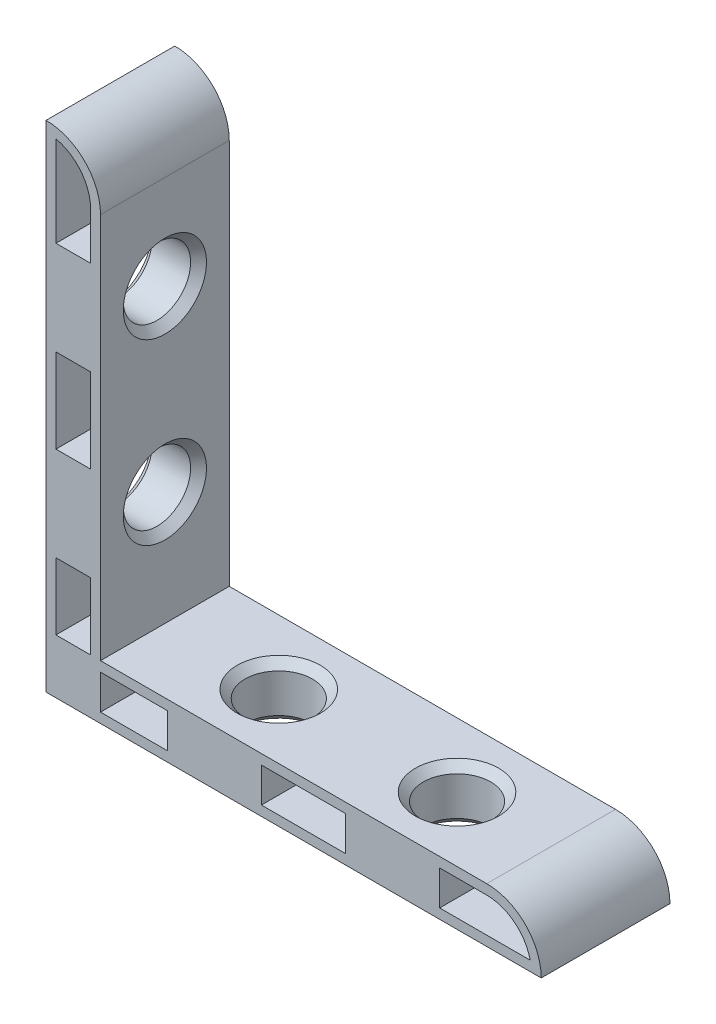
SolidWorks part; units mm, degrees
material "ЦА4М3 ГОСТ 25140-93"
ref_plane "Спереди" through (0, 0, 0) normal (0, 0, 1) x (1, 0, 0)
ref_plane "Сверху" through (0, 0, 0) normal (0, 1, 0) x (1, 0, 0)
ref_plane "Справа" through (0, 0, 0) normal (1, 0, 0) x (0, 0, -1)
sketch "Эскиз1" plane through (0, 0, 0) normal (0, 0, 1) x (1, 0, 0)
  line L0 (0, 50) -> (0, 0)
  line L1 (0, 0) -> (50, 0)
  line L2 (44.5, 5.5) -> (5.5, 5.5)
  line L3 (5.5, 5.5) -> (5.5, 44.5)
  line L4 (1, 48.8875) -> (1, 1)
  line L5 (1, 1) -> (48.8875, 1)
  line L6 (44.5, 4.5) -> (4.5, 4.5)
  line L7 (4.5, 4.5) -> (4.5, 44.5)
  arc A0 (50, 0) -> (44.5, 5.5) centre (44.5, 0) ccw
  arc A1 (5.5, 44.5) -> (0, 50) centre (0, 44.5) ccw
  arc A2 (48.8875, 1) -> (44.5, 4.5) centre (44.5, 0) ccw
  arc A3 (4.5, 44.5) -> (1, 48.8875) centre (0, 44.5) ccw
  point P9 (0, 0)
  dimension "D1" = 50
  dimension "D2" = 5.5
  dimension "D3" = 1
extrude "Бобышка-Вытянуть1" add sketch "Эскиз1" along normal mid plane 13
sketch "Эскиз2" plane through (0, 0, 0) normal (0, 0, 1) x (1, 0, 0)
  line L0 (0, 50) -> (0, 0) construction
  line L1 (5.5, 5.5) -> (0, 5.5)
  line L2 (5.5, 5.5) -> (5.5, 0)
  line L3 (5.5, 0) -> (0, 0)
  line L4 (0, 5.5) -> (0, 0)
  line L5 (0, 39.75) -> (5.5, 39.75)
  line L6 (0, 39.75) -> (0, 30.25)
  line L7 (0, 30.25) -> (5.5, 30.25)
  line L8 (5.5, 39.75) -> (5.5, 30.25)
  line L9 (5.5, 5.5) -> (5.5, 44.5) construction
  line L10 (0, 0) -> (24.8323, 24.8323) construction
  line L11 (0, 21.75) -> (5.5, 21.75)
  line L12 (0, 21.75) -> (0, 12.25)
  line L13 (0, 12.25) -> (5.5, 12.25)
  line L14 (5.5, 21.75) -> (5.5, 12.25)
  line L15 (21.75, 5.5) -> (12.25, 5.5)
  line L16 (12.25, 0) -> (12.25, 5.5)
  line L17 (21.75, 0) -> (12.25, 0)
  line L18 (21.75, 0) -> (21.75, 5.5)
  line L19 (39.75, 5.5) -> (30.25, 5.5)
  line L20 (30.25, 0) -> (30.25, 5.5)
  line L21 (39.75, 0) -> (30.25, 0)
  line L22 (39.75, 0) -> (39.75, 5.5)
  point P18 (0, 35)
  point P20 (0, 17)
  dimension "D1" = 15
  dimension "D2" = 9.5
  dimension "D3" = 18
extrude "Бобышка-Вытянуть2" add sketch "Эскиз2" along normal up to surface and the other way up to surface
sketch "Эскиз3" plane through (0, 0, 0) normal (0, 0, 1) x (1, 0, 0)
  line L4 (0, 0) -> (50, 0)
  line L5 (44.5, 5.5) -> (5.5, 5.5)
  line L6 (5.5, 5.5) -> (5.5, 44.5)
  line L7 (0, 50) -> (0, 0)
  line L8 (0, 0) -> (50, 0)
  line L9 (44.5, 5.5) -> (5.5, 5.5)
  line L10 (5.5, 5.5) -> (5.5, 44.5)
  line L11 (0, 50) -> (0, 0)
  arc A2 (50, 0) -> (44.5, 5.5) centre (44.5, 0) ccw
  arc A3 (5.5, 44.5) -> (0, 50) centre (0, 44.5) ccw
  arc A4 (50, 0) -> (44.5, 5.5) centre (44.5, 0) ccw
  arc A5 (5.5, 44.5) -> (0, 50) centre (0, 44.5) ccw
  dimension "D1" = 0
extrude "Бобышка-Вытянуть3" add sketch "Эскиз3" along normal mid plane 2
hole_wizard "Отверстие обработанное метчиком M81" positions "Эскиз4" profile "Эскиз5" tap size "M8" standard "ISO" end condition through all
sketch "Эскиз4" plane through (0, 0, 0) normal (-1, 0, 0) x (0, 0, 1)
  line L0 (6.5, 39.75) -> (6.5, 30.25)
  line L1 (6.5, 50) -> (6.5, 0) construction
  line L3 (1, 39.75) -> (6.5, 39.75) construction
  line L4 (6.5, 30.25) -> (1, 30.25) construction
  line L5 (6.5, 21.75) -> (6.5, 12.25)
  line L7 (1, 21.75) -> (6.5, 21.75) construction
  line L8 (6.5, 12.25) -> (1, 12.25) construction
  point P0 (0, 35)
  point P2 (0, 17)
  point P20 (6.5, 35)
  point P25 (0, 0)
  point P28 (0, 0)
  point P31 (6.5, 17)
  point P32 (-1.1124, 17)
  point P34 (0, 0)
sketch "Эскиз5" plane through (0, 35, 0) normal (0, 1, 0) x (0, 0, 1)
  line L0 (0, 0) -> (0, 5.5)
  line L1 (0, 5.5) -> (4.2, 5.5)
  line L2 (3.4, 4.7) -> (3.4, 0.8)
  line L3 (3.4, 0.8) -> (4.2, 0)
  line L5 (4.2, 0) -> (0, 0)
  line L6 (-3.4, 0.8) -> (-4.2, 0) construction
  line L7 (4.2, 5.5) -> (3.4, 4.7)
  line L8 (-4.2, 5.5) -> (-3.4, 4.7) construction
  line L11 (0, -6.35) -> (0, 107.95) construction
  dimension "Диаметр проходного сверла" = 6.8
  dimension "Глубина проходного сверла" = 5.5
  dimension "Диаметр передней зенковки" = 8.4
  dimension "Угол передней зенковки" = 90
  dimension "Диаметр задней зенковки" = 8.4
  dimension "Угол задней зенковки" = 90
cosmetic thread "Отверстие резьбы1" parameters "D2"=8
cosmetic thread "Отверстие резьбы2" parameters "D2"=8
ref_plane "Плоскость1" through (0, 0, 0) normal (-0.7071, 0.7071, 0) x (0.7071, 0.7071, 0)
mirror "Зеркальное отражение1" about plane through (0, 0, 0) normal (-0.7071, 0.7071, 0) of "Отверстие обработанное метчиком M81"
